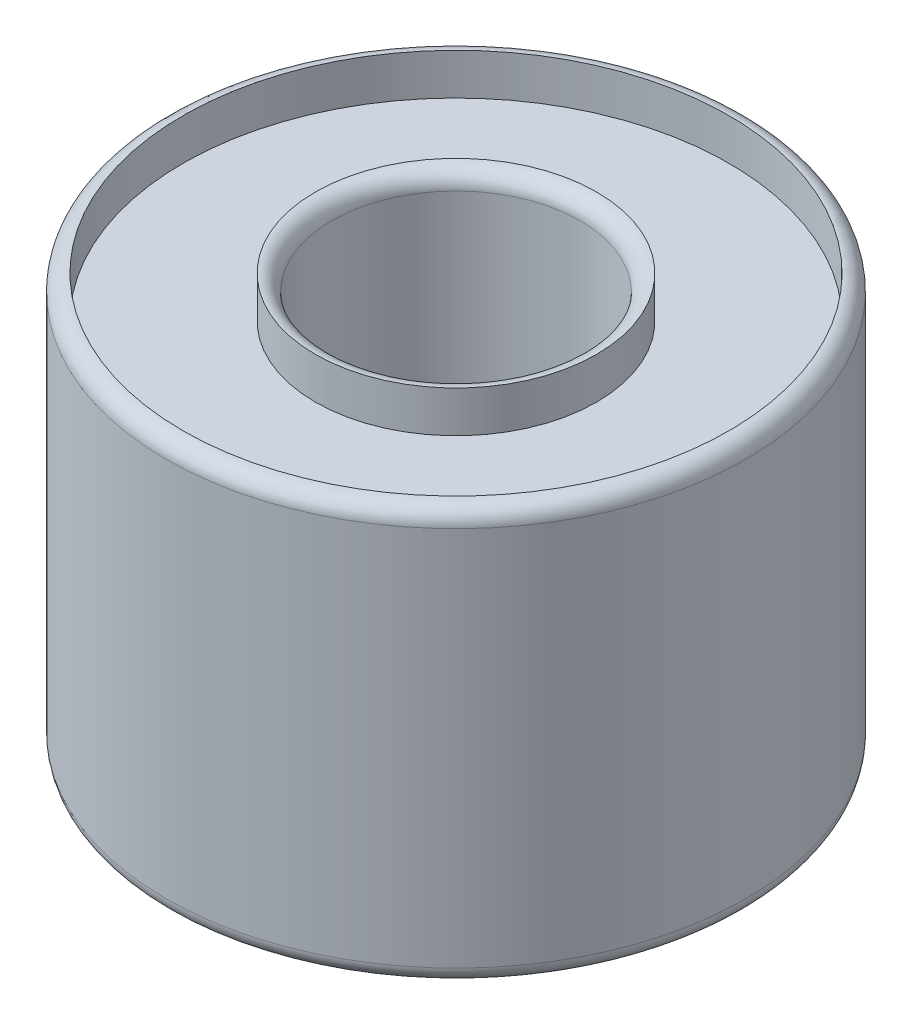
SolidWorks part; units mm, degrees
material "Acier inoxydable corroyé"
ref_plane "Plan de face" through (0, 0, 0) normal (0, 0, 1) x (1, 0, 0)
ref_plane "Plan de dessus" through (0, 0, 0) normal (0, 1, 0) x (1, 0, 0)
ref_plane "Plan de droite" through (0, 0, 0) normal (1, 0, 0) x (0, 0, -1)
sketch "Esquisse1" plane through (0, 0, 0) normal (0, 1, 0) x (1, 0, 0)
  circle A0 centre (0, 0) radius 3.5
  circle A1 centre (0, 0) radius 1.5
  dimension "D1" = 3
  dimension "D2" = 7
extrude "Boss.-Extru.1" add sketch "Esquisse1" along normal blind 5
fillet "Congé1" radius 0.2 4 edges at (0, 0, 1.5) (0, 0, 3.5) (0, 5, 1.5) (0, 5, 3.5)
sketch "Esquisse3" plane through (0, 5, 0) normal (0, 1, 0) x (1, 0, 0)
  circle A0 centre (0, 0) radius 3.3
  circle A1 centre (0, 0) radius 1.7
extrude "Enlèv. mat.-Extru.1" cut sketch "Esquisse3" against normal blind 0.5
sketch "Esquisse4" plane through (0, 0, 0) normal (0, -1, 0) x (1, 0, 0)
  circle A0 centre (0, 0) radius 1.7
  circle A1 centre (0, 0) radius 3.3
extrude "Enlèv. mat.-Extru.2" cut sketch "Esquisse4" against normal blind 0.5
